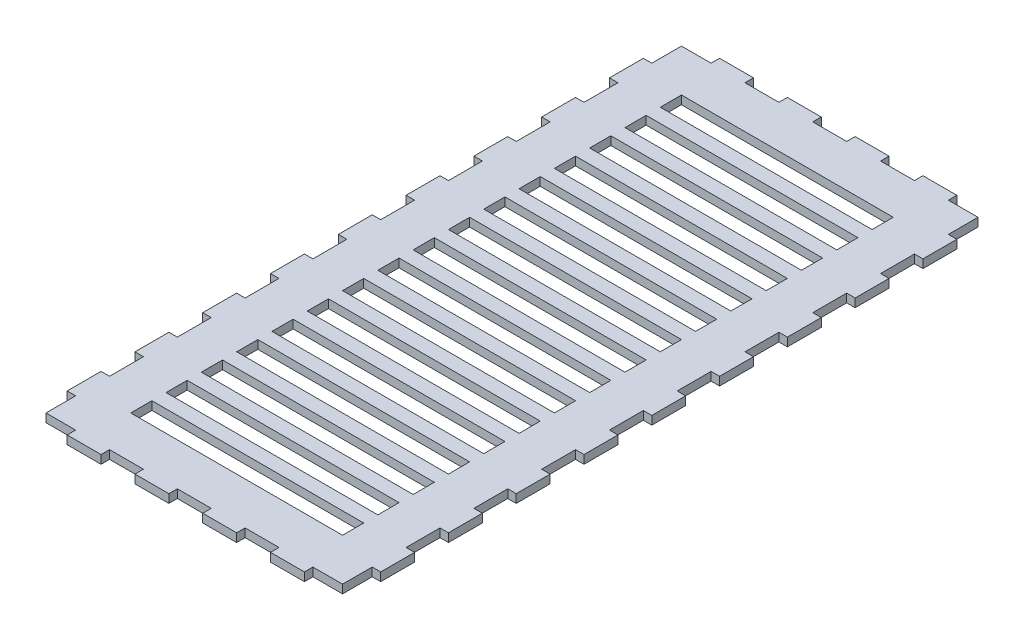
SolidWorks part; units mm, degrees
ref_plane "Front Plane" through (0, 0, 0) normal (0, 0, 1) x (1, 0, 0)
ref_plane "Top Plane" through (0, 0, 0) normal (0, 1, 0) x (1, 0, 0)
ref_plane "Right Plane" through (0, 0, 0) normal (1, 0, 0) x (0, 0, -1)
sketch "Sketch1" plane through (0, 0, 0) normal (0, 1, 0) x (1, 0, 0)
  line L0 (-75, -170) -> (-75, -155)
  line L1 (-105, -225) -> (105, -225)
  line L2 (-105, -225) -> (-105, 225)
  line L3 (-105, 225) -> (105, 225)
  line L4 (105, -225) -> (105, 225)
  line L5 (-105, -225) -> (105, 225) construction
  line L6 (-105, 225) -> (105, -225) construction
  line L7 (-75, -195) -> (75, -195)
  line L8 (-75, -195) -> (-75, -180)
  line L9 (-75, -180) -> (75, -180)
  line L10 (75, -195) -> (75, -180)
  line L11 (-75, -170) -> (75, -170)
  line L12 (75, -170) -> (75, -155)
  line L13 (-75, -155) -> (75, -155)
  line L14 (-75, -145) -> (-75, -130)
  line L15 (-75, -145) -> (75, -145)
  line L16 (75, -145) -> (75, -130)
  line L17 (-75, -130) -> (75, -130)
  line L18 (-75, -120) -> (-75, -105)
  line L19 (-75, -120) -> (75, -120)
  line L20 (75, -120) -> (75, -105)
  line L21 (-75, -105) -> (75, -105)
  line L22 (-75, -95) -> (-75, -80)
  line L23 (-75, -95) -> (75, -95)
  line L24 (75, -95) -> (75, -80)
  line L25 (-75, -80) -> (75, -80)
  line L26 (-75, -70) -> (-75, -55)
  line L27 (-75, -70) -> (75, -70)
  line L28 (75, -70) -> (75, -55)
  line L29 (-75, -55) -> (75, -55)
  line L30 (-75, -45) -> (-75, -30)
  line L31 (-75, -45) -> (75, -45)
  line L32 (75, -45) -> (75, -30)
  line L33 (-75, -30) -> (75, -30)
  line L34 (-75, -20) -> (-75, -5)
  line L35 (-75, -20) -> (75, -20)
  line L36 (75, -20) -> (75, -5)
  line L37 (-75, -5) -> (75, -5)
  line L38 (-75, 5) -> (-75, 20)
  line L39 (-75, 5) -> (75, 5)
  line L40 (75, 5) -> (75, 20)
  line L41 (-75, 20) -> (75, 20)
  line L42 (-75, 30) -> (-75, 45)
  line L43 (-75, 30) -> (75, 30)
  line L44 (75, 30) -> (75, 45)
  line L45 (-75, 45) -> (75, 45)
  line L46 (-75, 55) -> (-75, 70)
  line L47 (-75, 55) -> (75, 55)
  line L48 (75, 55) -> (75, 70)
  line L49 (-75, 70) -> (75, 70)
  line L50 (-75, 80) -> (-75, 95)
  line L51 (-75, 80) -> (75, 80)
  line L52 (75, 80) -> (75, 95)
  line L53 (-75, 95) -> (75, 95)
  line L54 (-75, 105) -> (-75, 120)
  line L55 (-75, 105) -> (75, 105)
  line L56 (75, 105) -> (75, 120)
  line L57 (-75, 120) -> (75, 120)
  line L58 (-75, 130) -> (-75, 145)
  line L59 (-75, 130) -> (75, 130)
  line L60 (75, 130) -> (75, 145)
  line L61 (-75, 145) -> (75, 145)
  line L62 (-75, 155) -> (-75, 170)
  line L63 (-75, 155) -> (75, 155)
  line L64 (75, 155) -> (75, 170)
  line L65 (-75, 170) -> (75, 170)
  line L66 (-75, 180) -> (-75, 195)
  line L67 (-75, 180) -> (75, 180)
  line L68 (75, 180) -> (75, 195)
  line L69 (-75, 195) -> (75, 195)
  point P0 (0, 0)
  dimension "D1" = 30
  dimension "D2" = 30
  dimension "D3" = 30
  dimension "D4" = 15
  dimension "D5" = 150
  dimension "D7" = 30
  dimension "D8" = 10
  dimension "D6" = 16
extrude "Boss-Extrude1" add sketch "Sketch1" along normal blind 6
sketch "Sketch2" plane through (0, 6, 0) normal (0, 1, 0) x (1, 0, 0)
  line L0 (105, 225) -> (-105, 225) construction
  line L1 (-84, 225) -> (-60, 225)
  line L2 (-84, 225) -> (-84, 231)
  line L3 (-84, 231) -> (-60, 231)
  line L4 (-60, 225) -> (-60, 231)
  line L5 (-36, 225) -> (-36, 231)
  line L6 (-36, 225) -> (-12, 225)
  line L7 (-12, 225) -> (-12, 231)
  line L8 (-36, 231) -> (-12, 231)
  line L9 (12, 225) -> (12, 231)
  line L10 (12, 225) -> (36, 225)
  line L11 (36, 225) -> (36, 231)
  line L12 (12, 231) -> (36, 231)
  line L13 (60, 225) -> (60, 231)
  line L14 (60, 225) -> (84, 225)
  line L15 (84, 225) -> (84, 231)
  line L16 (60, 231) -> (84, 231)
  line L17 (-36, -231) -> (-36, -225)
  line L18 (-36, -231) -> (-12, -231)
  line L19 (-12, -231) -> (-12, -225)
  line L20 (-36, -225) -> (-12, -225)
  line L21 (12, -231) -> (12, -225)
  line L22 (12, -231) -> (36, -231)
  line L23 (36, -231) -> (36, -225)
  line L24 (12, -225) -> (36, -225)
  line L25 (60, -231) -> (60, -225)
  line L26 (60, -231) -> (84, -231)
  line L27 (84, -231) -> (84, -225)
  line L28 (60, -225) -> (84, -225)
  line L29 (-84, -231) -> (-84, -225)
  line L30 (-84, -231) -> (-60, -231)
  line L31 (-60, -231) -> (-60, -225)
  line L32 (-84, -225) -> (-60, -225)
  line L33 (-84, 225) -> (-84, -231) construction
  line L34 (-12, 225) -> (12, 225)
  line L35 (-12, -225) -> (12, -225)
  line L38 (105, -225) -> (105, 225) construction
  point P6 (0, 225)
  point P7 (-72, 225)
  point P8 (0, -225)
  point P39 (0, 0)
  point P40 (0, 0)
  point P41 (0, 0)
  point P42 (0, 0)
  point P43 (0, 0)
  point P44 (0, 0)
  point P45 (0, 0)
  point P46 (0, 0)
  point P47 (0, 0)
  point P48 (0, 0)
  dimension "D1" = 6
  dimension "D2" = 24
  dimension "D5" = 456
  dimension "D6" = 24
  dimension "D7" = 450
  dimension "D3" = 4
  dimension "D4" = 2
sketch "Sketch3" plane through (0, 6, 0) normal (0, 1, 0) x (1, 0, 0)
  line L0 (-105, 225) -> (-105, -225) construction
  line L1 (-105, 204) -> (-111, 204)
  line L2 (-105, 204) -> (-105, 180)
  line L3 (-105, 180) -> (-111, 180)
  line L4 (-111, 204) -> (-111, 180)
  line L5 (111, 204) -> (111, 180)
  line L6 (111, 204) -> (105, 204)
  line L7 (105, 204) -> (105, 180)
  line L8 (111, 180) -> (105, 180)
  line L9 (111, 156) -> (111, 132)
  line L10 (111, 156) -> (105, 156)
  line L11 (105, 156) -> (105, 132)
  line L12 (111, 132) -> (105, 132)
  line L13 (111, 108) -> (111, 84)
  line L14 (111, 108) -> (105, 108)
  line L15 (105, 108) -> (105, 84)
  line L16 (111, 84) -> (105, 84)
  line L17 (111, 60) -> (111, 36)
  line L18 (111, 60) -> (105, 60)
  line L19 (105, 60) -> (105, 36)
  line L20 (111, 36) -> (105, 36)
  line L21 (111, 12) -> (111, -12)
  line L22 (111, 12) -> (105, 12)
  line L23 (105, 12) -> (105, -12)
  line L24 (111, -12) -> (105, -12)
  line L25 (111, -36) -> (111, -60)
  line L26 (111, -36) -> (105, -36)
  line L27 (105, -36) -> (105, -60)
  line L28 (111, -60) -> (105, -60)
  line L29 (111, -84) -> (111, -108)
  line L30 (111, -84) -> (105, -84)
  line L31 (105, -84) -> (105, -108)
  line L32 (111, -108) -> (105, -108)
  line L33 (111, -132) -> (111, -156)
  line L34 (111, -132) -> (105, -132)
  line L35 (105, -132) -> (105, -156)
  line L36 (111, -156) -> (105, -156)
  line L37 (111, -180) -> (111, -204)
  line L38 (111, -180) -> (105, -180)
  line L39 (105, -180) -> (105, -204)
  line L40 (111, -204) -> (105, -204)
  line L41 (-105, 156) -> (-105, 132)
  line L42 (-105, 156) -> (-111, 156)
  line L43 (-111, 156) -> (-111, 132)
  line L44 (-105, 132) -> (-111, 132)
  line L45 (-105, 108) -> (-105, 84)
  line L46 (-105, 108) -> (-111, 108)
  line L47 (-111, 108) -> (-111, 84)
  line L48 (-105, 84) -> (-111, 84)
  line L49 (-105, 60) -> (-105, 36)
  line L50 (-105, 60) -> (-111, 60)
  line L51 (-111, 60) -> (-111, 36)
  line L52 (-105, 36) -> (-111, 36)
  line L53 (-105, 12) -> (-105, -12)
  line L54 (-105, 12) -> (-111, 12)
  line L55 (-111, 12) -> (-111, -12)
  line L56 (-105, -12) -> (-111, -12)
  line L57 (-105, -36) -> (-105, -60)
  line L58 (-105, -36) -> (-111, -36)
  line L59 (-111, -36) -> (-111, -60)
  line L60 (-105, -60) -> (-111, -60)
  line L61 (-105, -84) -> (-105, -108)
  line L62 (-105, -84) -> (-111, -84)
  line L63 (-111, -84) -> (-111, -108)
  line L64 (-105, -108) -> (-111, -108)
  line L65 (-105, -132) -> (-105, -156)
  line L66 (-105, -132) -> (-111, -132)
  line L67 (-111, -132) -> (-111, -156)
  line L68 (-105, -156) -> (-111, -156)
  line L69 (-105, -180) -> (-105, -204)
  line L70 (-105, -180) -> (-111, -180)
  line L71 (-111, -180) -> (-111, -204)
  line L72 (-105, -204) -> (-111, -204)
  point P7 (-105, 0)
  point P8 (0, 0)
  point P76 (0, 0)
  dimension "D1" = 6
  dimension "D2" = 24
  dimension "D3" = 2
  dimension "D4" = 9
extrude "Boss-Extrude3" add sketch "Sketch3" against normal blind 6
extrude "Boss-Extrude4" add sketch "Sketch2" against normal blind 6 contours L1 L4 L3 L2 | L8 L5 L6 L7 | L12 L9 L10 L11 | L16 L13 L14 L15 | L32 L29 L30 L31 | L20 L17 L18 L19 | L24 L21 L22 L23 | L28 L27 L26 L25
